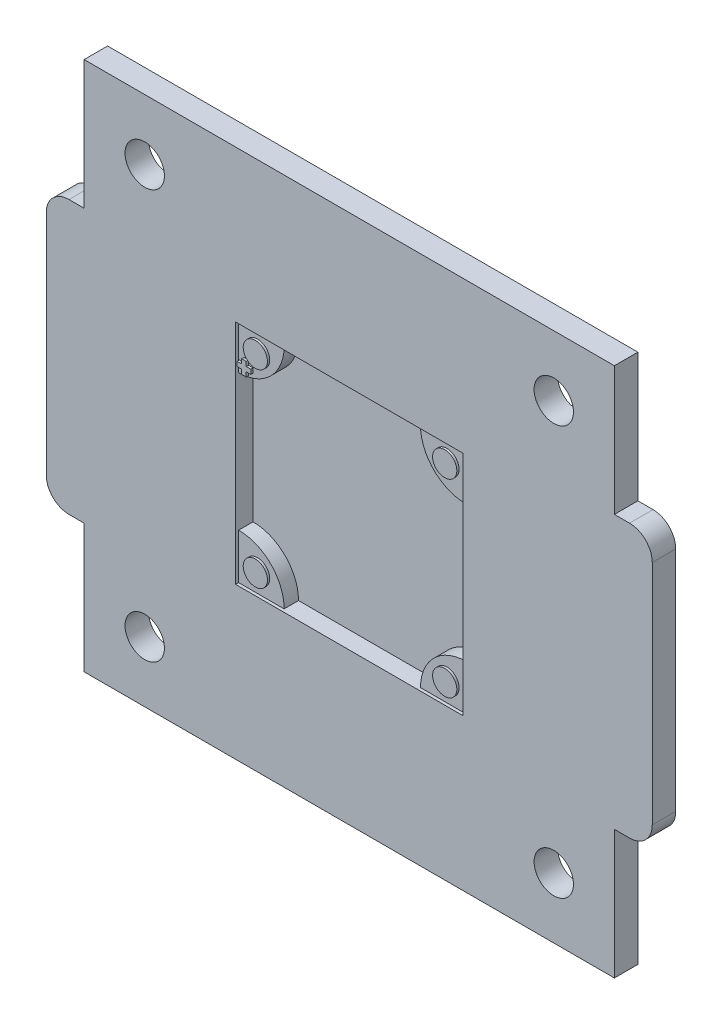
SolidWorks part; units mm, degrees
ref_plane "前视基准面" through (0, 0, 0) normal (0, 0, 1) x (1, 0, 0)
ref_plane "上视基准面" through (0, 0, 0) normal (0, 1, 0) x (1, 0, 0)
ref_plane "右视基准面" through (0, 0, 0) normal (1, 0, 0) x (0, 0, -1)
sketch "草图1" plane through (0, 0, 0) normal (0, 0, 1) x (1, 0, 0)
  line L0 (35, 70) -> (35, 0) construction
  line L1 (0, 0) -> (70, 0)
  line L2 (0, 0) -> (0, 70)
  line L3 (0, 70) -> (70, 70)
  line L4 (70, 0) -> (70, 70)
  line L5 (0, 35) -> (70, 35) construction
  line L6 (70, 17) -> (72, 17)
  line L7 (0, 53) -> (-2, 53)
  line L8 (0, 53) -> (0, 17)
  line L9 (0, 17) -> (-2, 17)
  line L10 (-5, 50) -> (-5, 20)
  line L11 (75, 50) -> (75, 20)
  line L12 (70, 53) -> (72, 53)
  line L13 (70, 53) -> (70, 17)
  arc A0 (-2, 17) -> (-5, 20) centre (-2, 20) cw
  arc A1 (-2, 53) -> (-5, 50) centre (-2, 50) ccw
  arc A2 (72, 17) -> (75, 20) centre (72, 20) ccw
  arc A3 (72, 53) -> (75, 50) centre (72, 50) cw
  point P6 (35, 70)
  point P10 (0, 35)
  point P15 (-5, 35)
  point P18 (-5, 17)
  point P21 (-5, 53)
  dimension "D4" = 3
  dimension "D1" = 70
  dimension "D2" = 5
  dimension "D3" = 36
extrude "凸台-拉伸1" add sketch "草图1" along normal blind 3.1 contours L7 A1 L10 A0 L9 L2 | L1 L4 L3 L2 | A3 L12 L4 L6 A2 L11
sketch "草图2" plane through (0, 0, 3.1) normal (0, 0, 1) x (1, 0, 0)
  line L0 (0, 70) -> (70, 70) construction
  line L1 (35, 70) -> (35, 0) construction
  line L2 (0, 0) -> (70, 0) construction
  line L3 (-5, 50) -> (-5, 20) construction
  line L4 (-5, 35) -> (75, 35) construction
  line L5 (75, 50) -> (75, 20) construction
  line L7 (20, 50) -> (50, 50)
  line L8 (20, 50) -> (20, 20)
  line L9 (20, 20) -> (50, 20)
  line L10 (50, 50) -> (50, 20)
  point P6 (35, 70)
  point P17 (35, 50)
  point P18 (20, 35)
  dimension "D1" = 30
extrude "切除-拉伸1" cut sketch "草图2" against normal blind 2.3
sketch "草图3" plane through (0, 0, 3.1) normal (0, 0, 1) x (1, 0, 0)
  line L0 (0, 70) -> (0, 0) construction
  line L1 (0, 70) -> (70, 70) construction
  line L2 (0, 53) -> (0, 70) construction
  line L3 (70, 0) -> (70, 70) construction
  line L4 (70, 53) -> (70, 70) construction
  line L5 (0, 35) -> (70, 35) construction
  line L6 (35, 70) -> (35, 0) construction
  line L7 (0, 0) -> (70, 0) construction
  circle A0 centre (8, 62) radius 2.6
  circle A1 centre (62, 62) radius 2.6
  circle A2 centre (8, 8) radius 2.6
  circle A3 centre (62, 8) radius 2.6
  point P18 (35, 70)
  point P19 (0, 35)
  dimension "D3" = 5.2
  dimension "D1" = 8
  dimension "D2" = 8
extrude "切除-拉伸2" cut sketch "草图3" against normal through all
sketch "草图4" plane through (0, 0, 0) normal (0, 0, 1) x (1, 0, 0)
  line L0 (20, 35) -> (50, 35) construction
  line L1 (20, 50) -> (50, 50) construction
  line L2 (20, 50) -> (20, 20) construction
  line L3 (20, 20) -> (50, 20) construction
  line L4 (50, 50) -> (50, 20) construction
  line L5 (35, 50) -> (35, 20) construction
  line L6 (20, 44) -> (20, 50)
  line L7 (20, 50) -> (26, 50)
  line L8 (50, 44) -> (50, 50)
  line L9 (50, 50) -> (44, 50)
  line L10 (50, 20) -> (44, 20)
  line L11 (50, 26) -> (50, 20)
  line L12 (20, 26) -> (20, 20)
  line L13 (20, 20) -> (26, 20)
  arc A0 (26, 50) -> (20, 44) centre (20, 50) cw
  arc A1 (44, 50) -> (50, 44) centre (50, 50) ccw
  arc A2 (44, 20) -> (50, 26) centre (50, 20) cw
  arc A3 (26, 20) -> (20, 26) centre (20, 20) ccw
  point P10 (35, 20)
  point P11 (20, 35)
  dimension "D1" = 6
extrude "凸台-拉伸2" add sketch "草图4" along normal blind 2.7
sketch "草图6" plane through (0, 0, 2.7) normal (0, 0, 1) x (1, 0, 0)
  line L0 (20, 35) -> (50, 35) construction
  line L1 (20, 50) -> (50, 50) construction
  line L2 (20, 50) -> (20, 20) construction
  line L3 (20, 20) -> (50, 20) construction
  line L4 (50, 50) -> (50, 20) construction
  line L5 (35, 50) -> (35, 20) construction
  line L6 (20.1, 45.5) -> (20.7, 45.5)
  line L7 (20.7, 45.5) -> (20.7, 46.1)
  line L8 (20.7, 46.1) -> (21.3, 46.1)
  line L9 (21.3, 46.1) -> (21.3, 45.5)
  line L10 (21.3, 45.5) -> (21.9, 45.5)
  line L11 (21.9, 45.5) -> (21.9, 44.9)
  line L12 (21.9, 44.9) -> (21.3, 44.9)
  line L13 (21.3, 44.9) -> (21.3, 44.3)
  line L14 (21.3, 44.3) -> (20.7, 44.3)
  line L15 (20.7, 44.3) -> (20.7, 44.9)
  line L16 (20.7, 44.9) -> (20.1, 44.9)
  line L17 (20.1, 44.9) -> (20.1, 45.5)
  circle A4 centre (22.5, 47.5) radius 1.6
  circle A5 centre (47.5, 47.5) radius 1.6
  circle A6 centre (47.5, 22.5) radius 1.6
  circle A7 centre (22.5, 22.5) radius 1.6
  point P10 (35, 20)
  point P11 (20, 35)
  point P31 (21, 46.1)
  dimension "D1" = 2.5
  dimension "D2" = 2.5
  dimension "D3" = 3.2
  dimension "D4" = 0.6
  dimension "D5" = 0.6
  dimension "D6" = 0.1
  dimension "D7" = 3.9
extrude "凸台-拉伸3" add sketch "草图6" along normal blind 0.3
